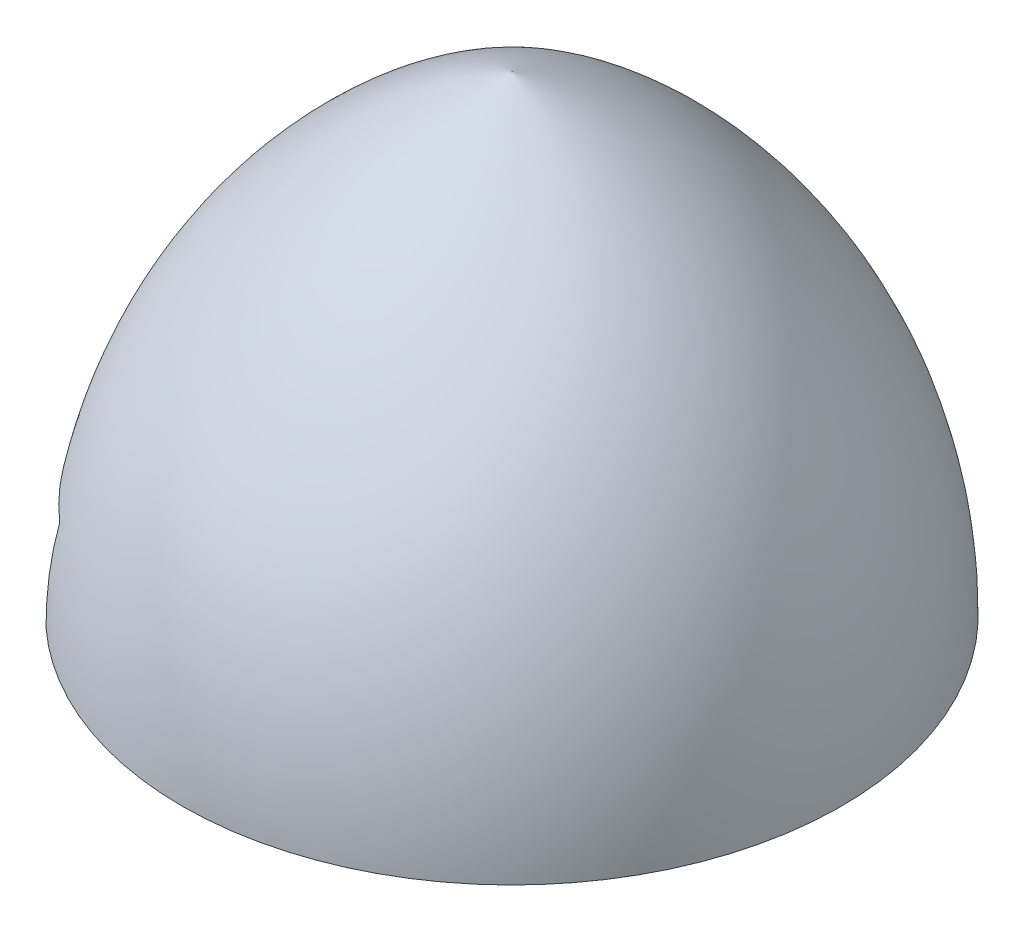
SolidWorks part; units mm, degrees
ref_plane "Front Plane" through (0, 0, 0) normal (0, 0, 1) x (1, 0, 0)
ref_plane "Top Plane" through (0, 0, 0) normal (0, 1, 0) x (1, 0, 0)
ref_plane "Right Plane" through (0, 0, 0) normal (1, 0, 0) x (0, 0, -1)
sketch "Sketch1" plane through (0, 0, 0) normal (1, 0, 0) x (0, 0, -1)
  line L0 (0, 5) -> (0, 0)
  line L1 (0, 0) -> (-3.5, 0)
  line L2 (0, 0) -> (0, -1.2045) construction
  arc A0 (-3.5, 0) -> (0, 5) centre (1.8214, 0) cw
  point P6 (0, 0)
  point P7 (5.1923, 1.9207)
  point P8 (0, 0)
  point P9 (0, 0)
  point P10 (0, 0)
  point P11 (0, 0)
  dimension "D1" = 7
  dimension "D2" = 5
revolve "Revolve1" add sketch "Sketch1" angle 360 about L2
sketch "Sketch2" plane through (0, 0, 0) normal (0, -1, 0) x (1, 0, 0)
  circle A0 centre (0, 0) radius 1
  dimension "D1" = 2
extrude "Cut-Extrude1" cut sketch "Sketch2" against normal blind 4
chamfer "Chamfer1" distance 1 angle 45 1 edges at (0, 4, -1)
sketch "Sketch4" plane through (0, 0, 0) normal (0, 1, 0) x (1, 0, 0)
  line L0 (-3.5, 2.75) -> (1, 2.0775)
  line L1 (1, -2.0775) -> (-3.5, -2.75)
  line L2 (-3.5, 2.75) -> (-0.0297, 2.75) construction
  line L3 (-2.75, 0) -> (2.75, 0) construction
  line L4 (-0.4188, 0) -> (-3.5, 0) construction
  line L5 (-3.5, 2.75) -> (-3.5, 0.75)
  line L6 (-3.5, -0.75) -> (-3.5, -2.75)
  line L7 (-3.5, 0) -> (-3.5, -0.75) construction
  line L8 (-3.5, 0.75) -> (-3.5, 0) construction
  arc A1 (1, 2.0775) -> (1, -2.0775) centre (0.6895, 0) cw
  circle A2 centre (0, 0) radius 3.5 construction
  arc A3 (-3.5, 0.75) -> (-3.5, -0.75) centre (-3.5, 0) cw
  point P6 (0, 0)
  dimension "D4" = 0.75
  dimension "D1" = 5.5
  dimension "D2" = 8.5
  dimension "D3" = 4.5
extrude "Cut-Extrude4" cut sketch "Sketch4" along normal blind 1.02
